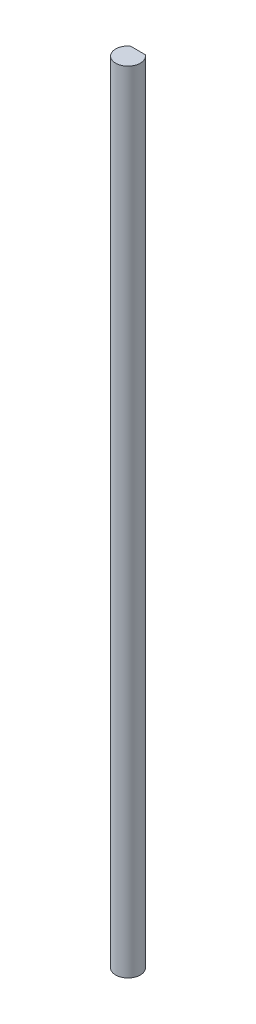
SolidWorks part; units mm, degrees
ref_plane "Front Plane" through (0, 0, 0) normal (0, 0, 1) x (1, 0, 0)
ref_plane "Top Plane" through (0, 0, 0) normal (0, 1, 0) x (1, 0, 0)
ref_plane "Right Plane" through (0, 0, 0) normal (1, 0, 0) x (0, 0, -1)
sketch "Sketch1" plane through (0, 0, 0) normal (0, 1, 0) x (1, 0, 0)
  line L0 (-1.905, 2.54) -> (1.905, 2.54)
  arc A0 (-1.905, 2.54) -> (1.905, 2.54) centre (0, 0) ccw
  dimension "D1" = 6.35
  dimension "D2" = 2.54
extrude "Boss-Extrude1" add sketch "Sketch1" along normal blind 203.2
